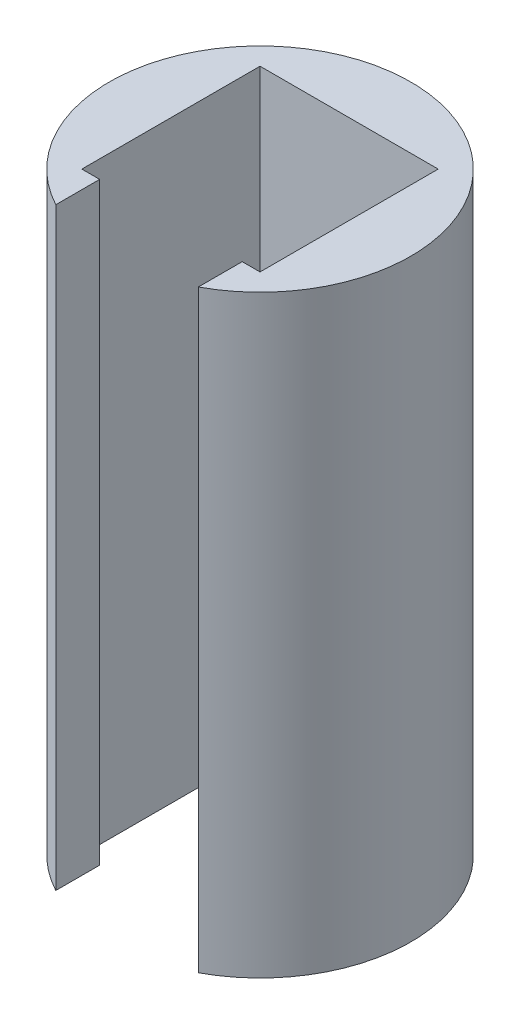
SolidWorks part; units mm, degrees
ref_plane "Front Plane" through (0, 0, 0) normal (0, 0, 1) x (1, 0, 0)
ref_plane "Top Plane" through (0, 0, 0) normal (0, 1, 0) x (1, 0, 0)
ref_plane "Right Plane" through (0, 0, 0) normal (1, 0, 0) x (0, 0, -1)
sketch "Sketch1" plane through (0, 0, 0) normal (0, 1, 0) x (1, 0, 0)
  line L0 (5.9996, -7.5) -> (7.5, -7.5)
  line L1 (-7.5, 7.5) -> (7.5, 7.5)
  line L2 (-7.5, 7.5) -> (-7.5, -7.5)
  line L3 (-7.5, -7.5) -> (-5.9996, -7.5)
  line L4 (7.5, 7.5) -> (7.5, -7.5)
  line L5 (-7.5, 7.5) -> (7.5, -7.5) construction
  line L6 (-7.5, -7.5) -> (7.5, 7.5) construction
  line L7 (-5.9996, -7.5) -> (-5.9996, -11.1935)
  line L9 (5.9996, -11.1935) -> (5.9996, -7.5)
  arc A0 (5.9996, -11.1935) -> (-5.9996, -11.1935) centre (0, 0) ccw
extrude "Boss-Extrude2" add sketch "Sketch1" along normal blind 50
